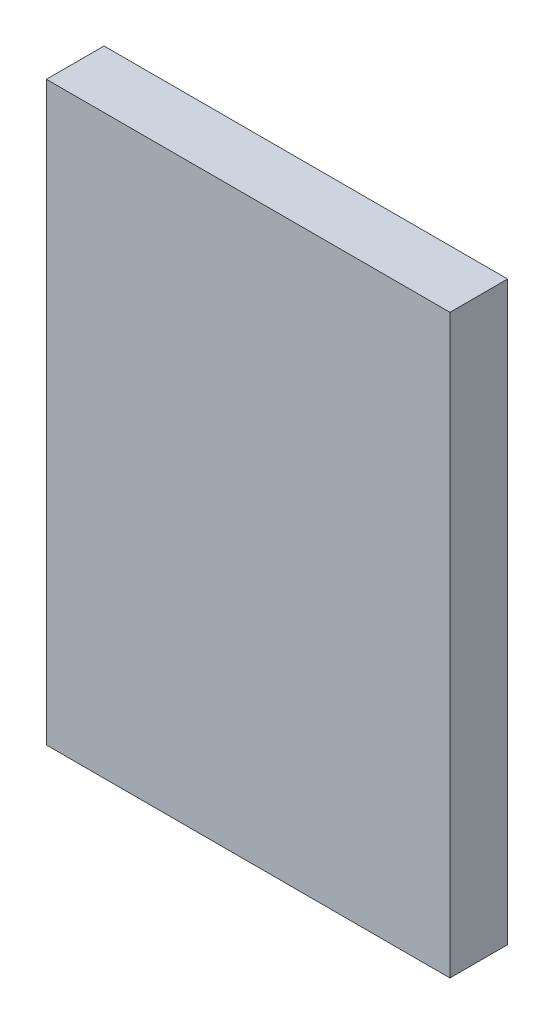
SolidWorks part; units mm, degrees
ref_plane "Front" through (0, 0, 0) normal (0, 0, 1) x (1, 0, 0)
ref_plane "Top" through (0, 0, 0) normal (0, 1, 0) x (1, 0, 0)
ref_plane "Right" through (0, 0, 0) normal (1, 0, 0) x (0, 0, -1)
sketch "Sketch1" plane through (0, 0, 0) normal (0, 0, 1) x (1, 0, 0)
  line L1 (175, -250) -> (-175, -250)
  line L2 (175, -250) -> (175, 250)
  line L3 (175, 250) -> (-175, 250)
  line L4 (-175, -250) -> (-175, 250)
  line L5 (175, -250) -> (-175, 250) construction
  line L6 (175, 250) -> (-175, -250) construction
  point P0 (0, 0)
  dimension "D1" = 500
  dimension "D2" = 350
extrude "Boss-Extrude1" add sketch "Sketch1" along normal mid plane 50
